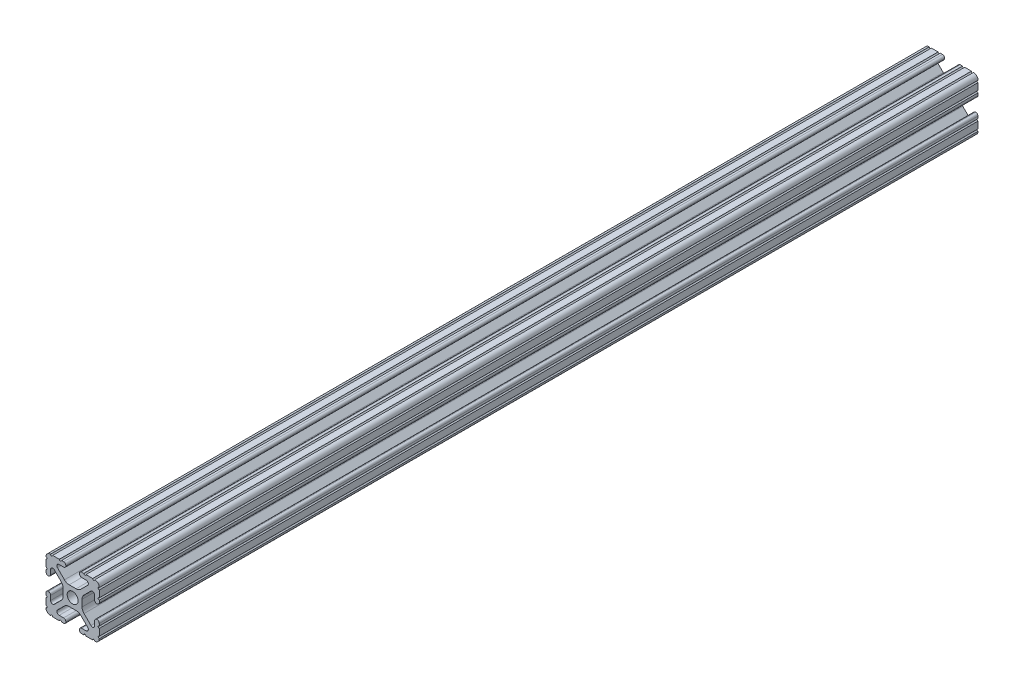
SolidWorks part; units mm, degrees
material "McMaster 6105-T5"
ref_plane "Front Plane" through (0, 0, 0) normal (0, 0, 1) x (1, 0, 0)
ref_plane "Top Plane" through (0, 0, 0) normal (0, 1, 0) x (1, 0, 0)
ref_plane "Right Plane" through (0, 0, 0) normal (1, 0, 0) x (0, 0, -1)
sketch "Sketch1" plane through (0, 0, 0) normal (0, 0, 1) x (1, 0, 0)
  line L88 (-7.1797, -8.6452) -> (-3.9523, -5.4237)
  line L89 (-1.7093, -4.4958) -> (1.7093, -4.4958)
  line L90 (3.9523, -5.4237) -> (7.1797, -8.6452)
  line L91 (6.4164, -10.4902) -> (4.2875, -10.4902)
  line L92 (3.2385, -11.5392) -> (3.2385, -11.651)
  line L93 (4.2875, -12.7) -> (5.3171, -12.7)
  line L94 (6.3331, -12.7) -> (9.5504, -12.7)
  line L95 (12.7, -9.5504) -> (12.7, -6.3331)
  line L96 (12.7, -5.3171) -> (12.7, -4.2875)
  line L97 (11.651, -3.2385) -> (11.5392, -3.2385)
  line L98 (10.4902, -4.2875) -> (10.4902, -6.4021)
  line L99 (8.7371, -7.1294) -> (5.441, -3.8408)
  line L100 (4.5085, -1.5932) -> (4.5085, 1.5932)
  line L101 (5.441, 3.8408) -> (8.7371, 7.1294)
  line L102 (10.4902, 6.4021) -> (10.4902, 4.2875)
  line L103 (11.5392, 3.2385) -> (11.651, 3.2385)
  line L104 (12.7, 4.2875) -> (12.7, 5.3171)
  line L105 (12.7, 6.3331) -> (12.7, 9.5504)
  line L106 (9.5504, 12.7) -> (6.3331, 12.7)
  line L107 (5.3171, 12.7) -> (4.2875, 12.7)
  line L108 (3.2385, 11.651) -> (3.2385, 11.5392)
  line L109 (4.2875, 10.4902) -> (6.4768, 10.4902)
  line L110 (7.207, 8.7244) -> (3.8983, 5.4232)
  line L111 (1.6558, 4.4958) -> (-1.6558, 4.4958)
  line L112 (-3.8983, 5.4232) -> (-7.207, 8.7244)
  line L113 (-6.4768, 10.4902) -> (-4.2875, 10.4902)
  line L114 (-3.2385, 11.5392) -> (-3.2385, 11.651)
  line L115 (-4.2875, 12.7) -> (-5.3171, 12.7)
  line L116 (-6.3331, 12.7) -> (-9.5504, 12.7)
  line L117 (-12.7, 9.5504) -> (-12.7, 6.3331)
  line L118 (-12.7, 5.3171) -> (-12.7, 4.2875)
  line L119 (-11.651, 3.2385) -> (-11.5392, 3.2385)
  line L120 (-10.4902, 4.2875) -> (-10.4902, 6.4021)
  line L121 (-8.7371, 7.1294) -> (-5.441, 3.8408)
  line L122 (-4.5085, 1.5932) -> (-4.5085, -1.5932)
  line L123 (-5.441, -3.8408) -> (-8.7371, -7.1294)
  line L124 (-10.4902, -6.4021) -> (-10.4902, -4.2875)
  line L125 (-11.5392, -3.2385) -> (-11.651, -3.2385)
  line L126 (-12.7, -4.2875) -> (-12.7, -5.3171)
  line L127 (-12.7, -6.3331) -> (-12.7, -9.5504)
  line L128 (-9.5504, -12.7) -> (-6.3331, -12.7)
  line L129 (-5.3171, -12.7) -> (-4.2875, -12.7)
  line L130 (-3.2385, -11.651) -> (-3.2385, -11.5392)
  line L131 (-4.2875, -10.4902) -> (-6.4164, -10.4902)
  circle A1 centre (0, 0) radius 2.6035
  arc A104 (-7.1797, -8.6452) -> (-6.4164, -10.4902) centre (-6.4164, -9.4098) ccw
  arc A105 (-1.7093, -4.4958) -> (-3.9523, -5.4237) centre (-1.7093, -7.6708) ccw
  arc A106 (3.9523, -5.4237) -> (1.7093, -4.4958) centre (1.7093, -7.6708) ccw
  arc A107 (6.4164, -10.4902) -> (7.1797, -8.6452) centre (6.4164, -9.4098) ccw
  arc A108 (4.2875, -10.4902) -> (3.2385, -11.5392) centre (4.2875, -11.5392) ccw
  arc A109 (3.2385, -11.651) -> (4.2875, -12.7) centre (4.2875, -11.651) ccw
  arc A110 (6.3331, -12.7) -> (5.3171, -12.7) centre (5.8251, -12.7) ccw
  arc A111 (10.5664, -12.6998) -> (9.5504, -12.7) centre (10.0584, -12.7) ccw
  arc A112 (10.5664, -12.6998) -> (12.6998, -10.5664) centre (10.5918, -10.5918) ccw
  arc A113 (12.7, -9.5504) -> (12.6998, -10.5664) centre (12.7, -10.0584) ccw
  arc A114 (12.7, -5.3171) -> (12.7, -6.3331) centre (12.7, -5.8251) ccw
  arc A115 (12.7, -4.2875) -> (11.651, -3.2385) centre (11.651, -4.2875) ccw
  arc A116 (11.5392, -3.2385) -> (10.4902, -4.2875) centre (11.5392, -4.2875) ccw
  arc A117 (8.7371, -7.1294) -> (10.4902, -6.4021) centre (9.4628, -6.4021) ccw
  arc A118 (4.5085, -1.5932) -> (5.441, -3.8408) centre (7.6835, -1.5932) ccw
  arc A119 (5.441, 3.8408) -> (4.5085, 1.5932) centre (7.6835, 1.5932) ccw
  arc A120 (10.4902, 6.4021) -> (8.7371, 7.1294) centre (9.4628, 6.4021) ccw
  arc A121 (10.4902, 4.2875) -> (11.5392, 3.2385) centre (11.5392, 4.2875) ccw
  arc A122 (11.651, 3.2385) -> (12.7, 4.2875) centre (11.651, 4.2875) ccw
  arc A123 (12.7, 6.3331) -> (12.7, 5.3171) centre (12.7, 5.8251) ccw
  arc A124 (12.6998, 10.5664) -> (12.7, 9.5504) centre (12.7, 10.0584) ccw
  arc A125 (12.6998, 10.5664) -> (10.5664, 12.6998) centre (10.5918, 10.5918) ccw
  arc A126 (9.5504, 12.7) -> (10.5664, 12.6998) centre (10.0584, 12.7) ccw
  arc A127 (5.3171, 12.7) -> (6.3331, 12.7) centre (5.8251, 12.7) ccw
  arc A128 (4.2875, 12.7) -> (3.2385, 11.651) centre (4.2875, 11.651) ccw
  arc A129 (3.2385, 11.5392) -> (4.2875, 10.4902) centre (4.2875, 11.5392) ccw
  arc A130 (7.207, 8.7244) -> (6.4768, 10.4902) centre (6.4768, 9.4563) ccw
  arc A131 (1.6558, 4.4958) -> (3.8983, 5.4232) centre (1.6558, 7.6708) ccw
  arc A132 (-3.8983, 5.4232) -> (-1.6558, 4.4958) centre (-1.6558, 7.6708) ccw
  arc A133 (-6.4768, 10.4902) -> (-7.207, 8.7244) centre (-6.4768, 9.4563) ccw
  arc A134 (-4.2875, 10.4902) -> (-3.2385, 11.5392) centre (-4.2875, 11.5392) ccw
  arc A135 (-3.2385, 11.651) -> (-4.2875, 12.7) centre (-4.2875, 11.651) ccw
  arc A136 (-6.3331, 12.7) -> (-5.3171, 12.7) centre (-5.8251, 12.7) ccw
  arc A137 (-10.5664, 12.6998) -> (-9.5504, 12.7) centre (-10.0584, 12.7) ccw
  arc A138 (-10.5664, 12.6998) -> (-12.6998, 10.5664) centre (-10.5918, 10.5918) ccw
  arc A139 (-12.7, 9.5504) -> (-12.6998, 10.5664) centre (-12.7, 10.0584) ccw
  arc A140 (-12.7, 5.3171) -> (-12.7, 6.3331) centre (-12.7, 5.8251) ccw
  arc A141 (-12.7, 4.2875) -> (-11.651, 3.2385) centre (-11.651, 4.2875) ccw
  arc A142 (-11.5392, 3.2385) -> (-10.4902, 4.2875) centre (-11.5392, 4.2875) ccw
  arc A143 (-8.7371, 7.1294) -> (-10.4902, 6.4021) centre (-9.4628, 6.4021) ccw
  arc A144 (-4.5085, 1.5932) -> (-5.441, 3.8408) centre (-7.6835, 1.5932) ccw
  arc A145 (-5.441, -3.8408) -> (-4.5085, -1.5932) centre (-7.6835, -1.5932) ccw
  arc A146 (-10.4902, -6.4021) -> (-8.7371, -7.1294) centre (-9.4628, -6.4021) ccw
  arc A147 (-10.4902, -4.2875) -> (-11.5392, -3.2385) centre (-11.5392, -4.2875) ccw
  arc A148 (-11.651, -3.2385) -> (-12.7, -4.2875) centre (-11.651, -4.2875) ccw
  arc A149 (-12.7, -6.3331) -> (-12.7, -5.3171) centre (-12.7, -5.8251) ccw
  arc A150 (-12.6998, -10.5664) -> (-12.7, -9.5504) centre (-12.7, -10.0584) ccw
  arc A151 (-12.6998, -10.5664) -> (-10.5664, -12.6998) centre (-10.5918, -10.5918) ccw
  arc A152 (-9.5504, -12.7) -> (-10.5664, -12.6998) centre (-10.0584, -12.7) ccw
  arc A153 (-5.3171, -12.7) -> (-6.3331, -12.7) centre (-5.8251, -12.7) ccw
  arc A154 (-4.2875, -12.7) -> (-3.2385, -11.651) centre (-4.2875, -11.651) ccw
  arc A155 (-3.2385, -11.5392) -> (-4.2875, -10.4902) centre (-4.2875, -11.5392) ccw
extrude "Boss-Extrude1" add sketch "Sketch1" along normal mid plane 419.1
sketch "Sketch2" plane through (0, 12.7, 0) normal (0, 1, 0) x (1, 0, 0)
  line L0 (0, -155.4789) -> (0, 151.1822) construction
  line L1 (1.6558, -209.55) -> (-1.6558, -209.55) construction
  line L2 (1.6558, 209.55) -> (-1.6558, 209.55) construction
  circle A0 centre (0, -146.05) radius 3.175
  circle A1 centre (0, 184.15) radius 3.175
  point P4 (0, -209.55)
  point P12 (0, 209.55)
  dimension "D3" = 6.35
  dimension "D1" = 63.5
  dimension "D2" = 25.4
extrude "Cut-Extrude1" [suppressed] cut sketch "Sketch2" against normal through all both and the other way through all
sketch "Sketch3" plane through (-12.7, 0, 0) normal (-1, 0, 0) x (0, 0, 1)
  line L0 (-144.1574, 0) -> (-126.6701, 0) construction
  line L2 (209.55, 1.5932) -> (209.55, -1.5932) construction
  line L3 (-209.55, 1.5932) -> (-209.55, -1.5932) construction
  circle A0 centre (-158.75, 0) radius 3.175
  circle A1 centre (120.65, 0) radius 3.175
  dimension "D1" = 6.35
  dimension "D2" = 88.9
  dimension "D3" = 50.8
extrude "Cut-Extrude2" [suppressed] cut sketch "Sketch3" against normal through all both and the other way through all
